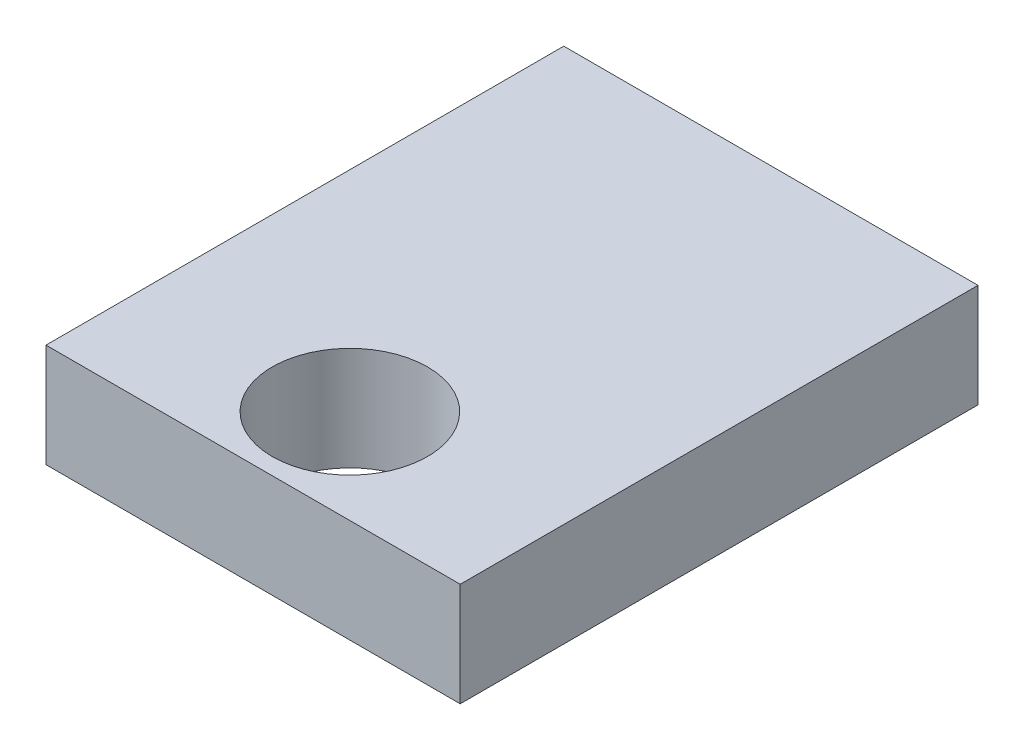
SolidWorks part; units mm, degrees
ref_plane "Alzado" through (0, 0, 0) normal (0, 0, 1) x (1, 0, 0)
ref_plane "Planta" through (0, 0, 0) normal (0, 1, 0) x (1, 0, 0)
ref_plane "Vista lateral" through (0, 0, 0) normal (1, 0, 0) x (0, 0, -1)
sketch "Croquis1" plane through (0, 0, 0) normal (0, 1, 0) x (1, 0, 0)
  line L1 (0, 0) -> (8, 0)
  line L2 (0, 0) -> (0, -10)
  line L3 (0, -10) -> (8, -10)
  line L4 (8, 0) -> (8, -10)
  circle A0 centre (4.0486, -8.18) radius 1.5
  dimension "D1" = 10
  dimension "D2" = 8
extrude "Saliente-Extruir1" add sketch "Croquis1" along normal blind 2
scale "Escala1" scale about centroid uniform scaling yes scale factor 7
